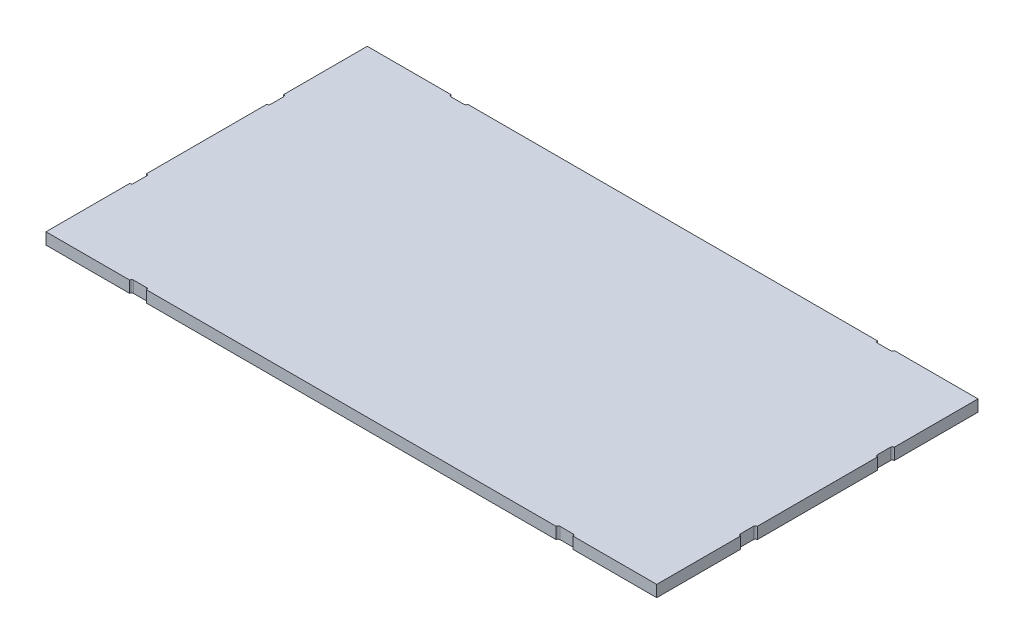
SolidWorks part; units mm, degrees
ref_plane "Front Plane" through (0, 0, 0) normal (0, 0, 1) x (1, 0, 0)
ref_plane "Top Plane" through (0, 0, 0) normal (0, 1, 0) x (1, 0, 0)
ref_plane "Right Plane" through (0, 0, 0) normal (1, 0, 0) x (0, 0, -1)
sketch "Sketch1" plane through (0, 0, 0) normal (0, 1, 0) x (1, 0, 0)
  line L1 (-316.5, 166.5) -> (316.5, 166.5)
  line L2 (-316.5, 166.5) -> (-316.5, -166.5)
  line L3 (-316.5, -166.5) -> (316.5, -166.5)
  line L4 (316.5, 166.5) -> (316.5, -166.5)
  line L5 (-316.5, 166.5) -> (316.5, -166.5) construction
  line L6 (-316.5, -166.5) -> (316.5, 166.5) construction
  point P0 (0, 0)
  dimension "LARGURA" = 633
  dimension "PROFUNDIDADE" = 333
extrude "Boss-Extrude1" add sketch "Sketch1" along normal blind 12
sketch "Sketch2" plane through (0, 12, 0) normal (0, 1, 0) x (1, 0, 0)
  line L0 (-316.5, -166.5) -> (316.5, -166.5) construction
  line L1 (-227.75, -164.5) -> (-214.25, -164.5)
  line L2 (-229.75, -166.5) -> (-229.75, -168.5)
  line L3 (-229.75, -168.5) -> (-212.25, -168.5)
  line L4 (-212.25, -166.5) -> (-212.25, -168.5)
  line L5 (-229.75, -164.5) -> (-212.25, -168.5) construction
  line L6 (-229.75, -168.5) -> (-212.25, -164.5) construction
  line L7 (-316.5, 166.5) -> (-316.5, -166.5) construction
  line L8 (0, -230.3274) -> (0, 199.7202) construction
  line L9 (-190.9314, 0) -> (209.2822, 0) construction
  line L10 (316.5, -166.5) -> (316.5, 166.5) construction
  line L11 (316.5, -62.25) -> (318.5, -62.25)
  line L12 (314.5, -64.25) -> (314.5, -77.75)
  line L13 (316.5, -79.75) -> (318.5, -79.75)
  line L14 (318.5, -62.25) -> (318.5, -79.75)
  line L15 (314.5, -62.25) -> (318.5, -79.75) construction
  line L16 (314.5, -79.75) -> (318.5, -62.25) construction
  line L17 (229.75, -168.5) -> (212.25, -164.5) construction
  line L18 (229.75, -164.5) -> (212.25, -168.5) construction
  line L19 (212.25, -166.5) -> (212.25, -168.5)
  line L20 (229.75, -168.5) -> (212.25, -168.5)
  line L21 (229.75, -166.5) -> (229.75, -168.5)
  line L22 (227.75, -164.5) -> (214.25, -164.5)
  line L23 (314.5, 79.75) -> (318.5, 62.25) construction
  line L24 (314.5, 62.25) -> (318.5, 79.75) construction
  line L25 (318.5, 62.25) -> (318.5, 79.75)
  line L26 (316.5, 79.75) -> (318.5, 79.75)
  line L27 (314.5, 64.25) -> (314.5, 77.75)
  line L28 (316.5, 62.25) -> (318.5, 62.25)
  line L29 (-314.5, 62.25) -> (-318.5, 79.75) construction
  line L30 (-314.5, 79.75) -> (-318.5, 62.25) construction
  line L31 (-316.5, 62.25) -> (-318.5, 62.25)
  line L32 (-314.5, 64.25) -> (-314.5, 77.75)
  line L33 (-316.5, 79.75) -> (-318.5, 79.75)
  line L34 (-318.5, 62.25) -> (-318.5, 79.75)
  line L35 (-314.5, -79.75) -> (-318.5, -62.25) construction
  line L36 (-314.5, -62.25) -> (-318.5, -79.75) construction
  line L37 (-318.5, -62.25) -> (-318.5, -79.75)
  line L38 (-316.5, -79.75) -> (-318.5, -79.75)
  line L39 (-314.5, -64.25) -> (-314.5, -77.75)
  line L40 (-316.5, -62.25) -> (-318.5, -62.25)
  line L41 (229.75, 164.5) -> (212.25, 168.5) construction
  line L42 (229.75, 168.5) -> (212.25, 164.5) construction
  line L43 (227.75, 164.5) -> (214.25, 164.5)
  line L44 (229.75, 166.5) -> (229.75, 168.5)
  line L45 (229.75, 168.5) -> (212.25, 168.5)
  line L46 (212.25, 166.5) -> (212.25, 168.5)
  line L47 (-229.75, 168.5) -> (-212.25, 164.5) construction
  line L48 (-229.75, 164.5) -> (-212.25, 168.5) construction
  line L49 (-212.25, 166.5) -> (-212.25, 168.5)
  line L50 (-229.75, 168.5) -> (-212.25, 168.5)
  line L51 (-229.75, 166.5) -> (-229.75, 168.5)
  line L52 (-227.75, 164.5) -> (-214.25, 164.5)
  arc A0 (-212.25, -166.5) -> (-214.25, -164.5) centre (-214.25, -166.5) ccw
  arc A1 (-227.75, -164.5) -> (-229.75, -166.5) centre (-227.75, -166.5) ccw
  arc A2 (314.5, -64.25) -> (316.5, -62.25) centre (316.5, -64.25) cw
  arc A3 (314.5, -77.75) -> (316.5, -79.75) centre (316.5, -77.75) ccw
  arc A4 (227.75, -164.5) -> (229.75, -166.5) centre (227.75, -166.5) cw
  arc A5 (212.25, -166.5) -> (214.25, -164.5) centre (214.25, -166.5) cw
  arc A6 (314.5, 77.75) -> (316.5, 79.75) centre (316.5, 77.75) cw
  arc A7 (314.5, 64.25) -> (316.5, 62.25) centre (316.5, 64.25) ccw
  arc A8 (-314.5, 64.25) -> (-316.5, 62.25) centre (-316.5, 64.25) cw
  arc A9 (-314.5, 77.75) -> (-316.5, 79.75) centre (-316.5, 77.75) ccw
  arc A10 (-314.5, -77.75) -> (-316.5, -79.75) centre (-316.5, -77.75) cw
  arc A11 (-314.5, -64.25) -> (-316.5, -62.25) centre (-316.5, -64.25) ccw
  arc A12 (212.25, 166.5) -> (214.25, 164.5) centre (214.25, 166.5) ccw
  arc A13 (227.75, 164.5) -> (229.75, 166.5) centre (227.75, 166.5) ccw
  arc A14 (-227.75, 164.5) -> (-229.75, 166.5) centre (-227.75, 166.5) cw
  arc A15 (-212.25, 166.5) -> (-214.25, 164.5) centre (-214.25, 166.5) cw
  point P0 (-221, -166.5)
  point P14 (316.5, -71)
  point P37 (221, -166.5)
  point P48 (316.5, 71)
  point P57 (-221, -166.5)
  point P66 (-316.5, 71)
  point P77 (-316.5, -71)
  point P88 (221, 166.5)
  point P99 (-221, 166.5)
  dimension "D7" = 2
  dimension "D8" = 2
  dimension "D1" = 17.5
  dimension "D2" = 2
  dimension "D3" = 95.5
  dimension "D4" = 2
  dimension "D5" = 17.5
  dimension "D6" = 95.5
extrude "Cut-Extrude1" cut sketch "Sketch2" against normal through all
